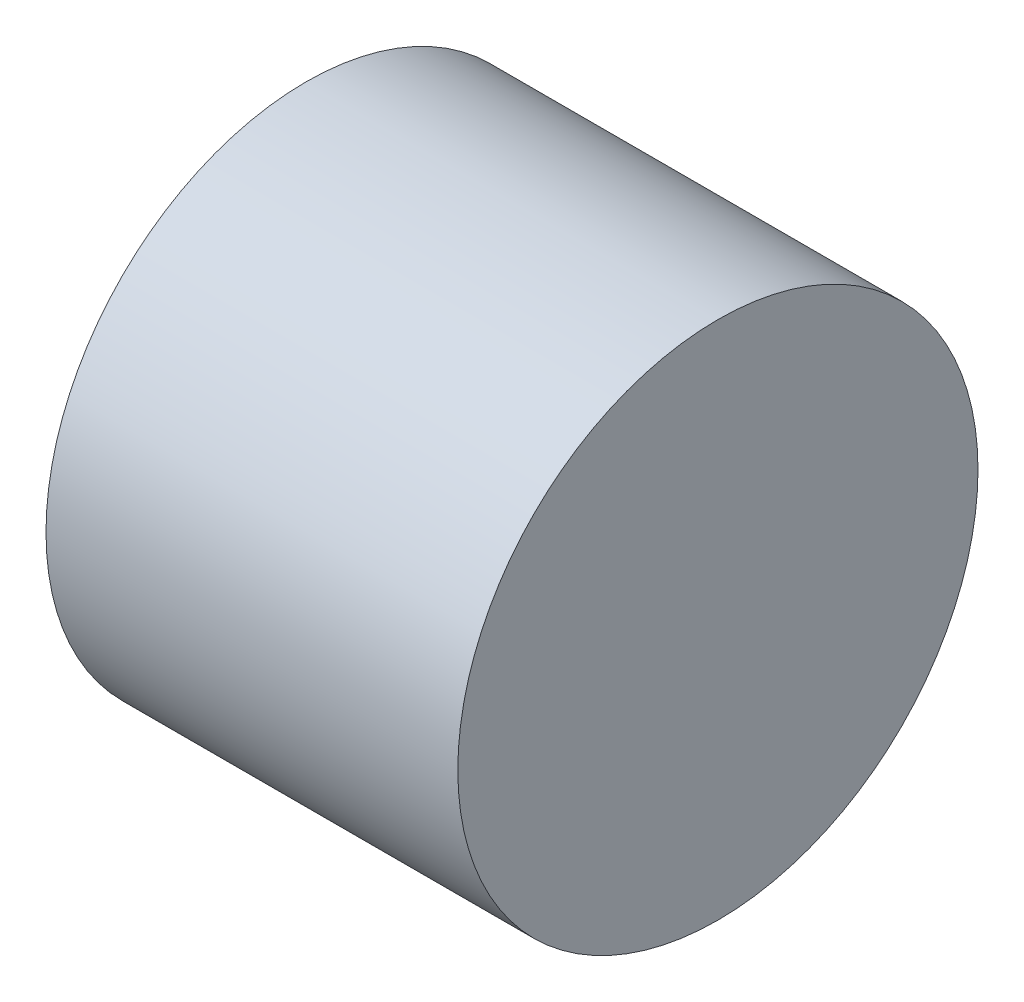
SolidWorks part; units mm, degrees
ref_plane "Front Plane" through (0, 0, 0) normal (0, 0, 1) x (1, 0, 0)
ref_plane "Top Plane" through (0, 0, 0) normal (0, 1, 0) x (1, 0, 0)
ref_plane "Right Plane" through (0, 0, 0) normal (1, 0, 0) x (0, 0, -1)
sketch "Sketch1" plane through (0, 0, 0) normal (1, 0, 0) x (0, 0, -1)
  circle A0 centre (0, 0) radius 6
  dimension "D1" = 12
extrude "Boss-Extrude1" add sketch "Sketch1" along normal blind 9.5
scale "Scale1" scale about centroid uniform scaling yes scale factor 25.4
